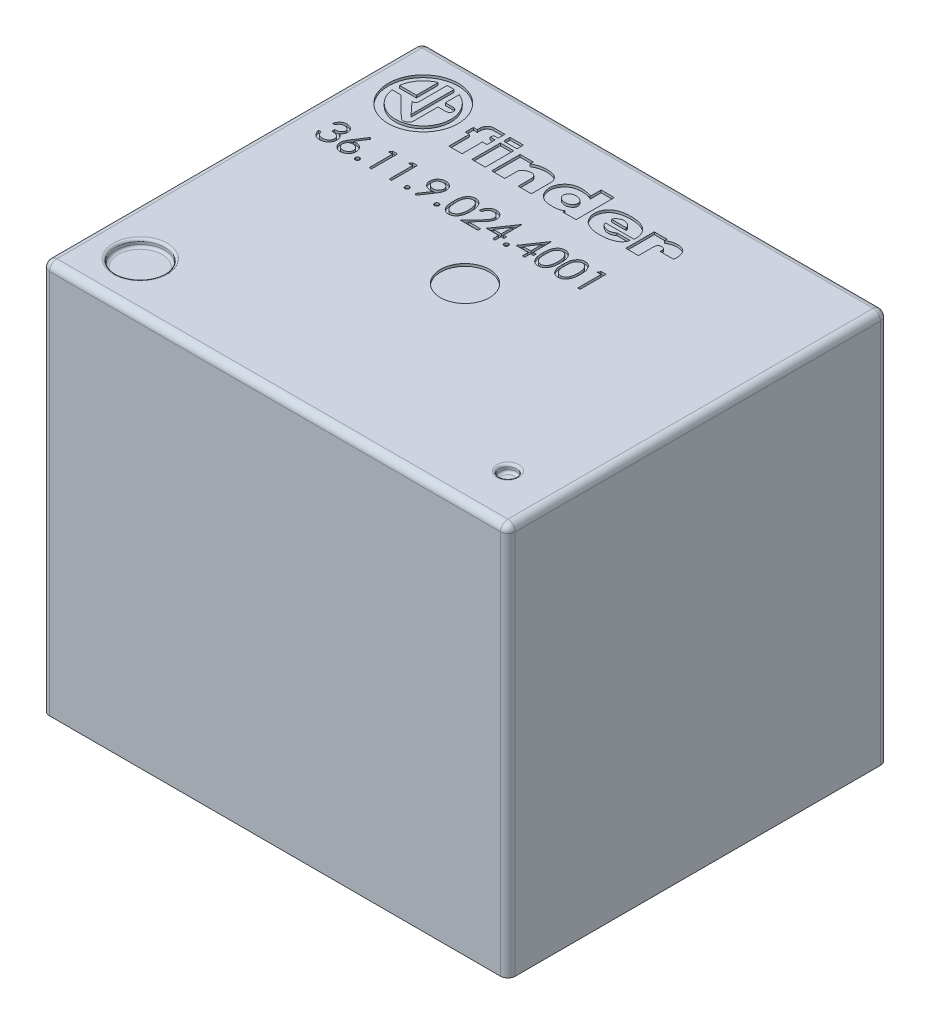
SolidWorks part; units mm, degrees
ref_plane "Front Plane" through (0, 0, 0) normal (0, 0, 1) x (1, 0, 0)
ref_plane "Top Plane" through (0, 0, 0) normal (0, 1, 0) x (1, 0, 0)
ref_plane "Right Plane" through (0, 0, 0) normal (1, 0, 0) x (0, 0, -1)
sketch "Sketch1" plane through (0, 0, 0) normal (0, 1, 0) x (1, 0, 0)
  line L0 (9.5, -7.75) -> (-9.5, 7.75) construction
  line L1 (-9.5, -7.75) -> (9.5, -7.75)
  line L2 (-9.5, -7.75) -> (-9.5, 7.75)
  line L3 (-9.5, 7.75) -> (9.5, 7.75)
  line L4 (9.5, -7.75) -> (9.5, 7.75)
  dimension "D1" = 19
  dimension "D2" = 15.5
extrude "Boss-Extrude1" add sketch "Sketch1" along normal blind 16
sketch "Sketch3" plane through (0, 0, 0) normal (0, -1, 0) x (1, 0, 0)
  line L0 (6.55, 5.75) -> (5.65, 6.25) construction
  line L1 (-6.35, 6.45) -> (-5.85, 6.45)
  line L2 (-6.35, 6.45) -> (-6.35, 5.55)
  line L3 (-6.35, 5.55) -> (-5.85, 5.55)
  line L4 (-5.85, 6.45) -> (-5.85, 5.55)
  line L5 (-8.35, 0.45) -> (-7.85, 0.45)
  line L6 (-8.35, 0.45) -> (-8.35, -0.45)
  line L7 (-8.35, -0.45) -> (-7.85, -0.45)
  line L8 (-7.85, 0.45) -> (-7.85, -0.45)
  line L9 (-6.35, -5.55) -> (-5.85, -5.55)
  line L10 (-6.35, -5.55) -> (-6.35, -6.45)
  line L11 (-6.35, -6.45) -> (-5.85, -6.45)
  line L12 (-5.85, -5.55) -> (-5.85, -6.45)
  line L13 (5.65, -6.25) -> (6.55, -6.25)
  line L14 (5.65, -6.25) -> (5.65, -5.75)
  line L15 (5.65, -5.75) -> (6.55, -5.75)
  line L16 (6.55, -6.25) -> (6.55, -5.75)
  line L17 (5.65, 6.25) -> (6.55, 6.25)
  line L18 (5.65, 6.25) -> (5.65, 5.75)
  line L19 (5.65, 5.75) -> (6.55, 5.75)
  line L20 (6.55, 6.25) -> (6.55, 5.75)
  line L21 (6.55, -5.75) -> (5.65, -6.25) construction
  line L22 (-5.85, 5.55) -> (-6.35, 6.45) construction
  line L23 (-7.85, -0.45) -> (-8.35, 0.45) construction
  line L24 (-5.85, -6.45) -> (-6.35, -5.55) construction
  line L25 (6.1, 6) -> (6.1, -6) construction
  line L26 (-6.1, 6) -> (-4.4393, 6) construction
  line L27 (-6.1, -6) -> (-4.066, -6) construction
  line L28 (-8.1, 0) -> (0, 0) construction
  line L29 (-6.1, 6) -> (-6.1, -6) construction
  line L30 (9.5, 7.75) -> (9.5, -7.75) construction
  dimension "D1" = 6
  dimension "D2" = 6
  dimension "D3" = 2
  dimension "D4" = 12.2
  dimension "D6" = 0.5
  dimension "D7" = 0.9
  dimension "D8" = 3.4
extrude "Boss-Extrude2" add sketch "Sketch3" along normal blind 1
fillet "Fillet1" radius 0.3 8 edges at (0, 16, -7.75) (9.5, 16, 0) (0, 16, 7.75) (-9.5, 16, 0) (-9.5, 8, -7.75) (-9.5, 8, 7.75) (9.5, 8, -7.75) (9.5, 8, 7.75)
sketch "Sketch4" plane through (0, 16, 0) normal (0, 1, 0) x (1, 0, 0)
  line L0 (7.5, -5.75) -> (-7.5, -5.75) construction
  line L1 (9.2, -7.75) -> (-9.2, -7.75) construction
  line L2 (-9.5, -7.45) -> (-9.5, 7.45) construction
  line L3 (9.5, 7.45) -> (9.5, -7.45) construction
  circle A0 centre (-7.5, -5.75) radius 1
  circle A1 centre (7.5, -5.75) radius 0.35
  dimension "D1" = 2
  dimension "D2" = 0.7
  dimension "D3" = 2
  dimension "D4" = 2
  dimension "D5" = 2
extrude "Cut-Extrude1" cut sketch "Sketch4" against normal blind 0.3
fillet "Fillet2" radius 0.1 4 edges at (7.5, 15.7, 6.1) (-7.5, 15.7, 6.75) (7.5, 16, 6.1) (-7.5, 16, 6.75)
sketch "Sketch5" plane through (0, 16, 0) normal (0, 1, 0) x (1, 0, 0)
  circle A0 centre (0, 0) radius 1
  dimension "D1" = 2
extrude "Cut-Extrude2" cut sketch "Sketch5" against normal blind 0.1
sketch "Sketch6" plane through (0, 16, 0) normal (0, 1, 0) x (1, 0, 0)
  line L0 (-7.0766, 6.631) -> (-7.0766, 4.8774)
  line L1 (-7.0766, 4.8774) -> (-7.5192, 5.3576)
  line L2 (-7.5192, 5.3576) -> (-7.4506, 5.3576)
  line L3 (-7.3614, 5.4643) -> (-7.3614, 6.6301)
  line L4 (-7.6461, 6.5542) -> (-7.6461, 5.663)
  line L5 (-7.6461, 5.663) -> (-8.3331, 5.663)
  line L6 (-8.3326, 5.3576) -> (-7.972, 5.3576)
  line L7 (-7.972, 5.3576) -> (-7.1334, 4.5348)
  line L8 (-6.7885, 4.6853) -> (-6.7885, 5.6868)
  line L9 (-6.7885, 5.6868) -> (-6.4489, 5.6868)
  line L10 (-6.4794, 5.9853) -> (-6.7885, 5.9853)
  line L11 (-6.7885, 5.9853) -> (-6.7885, 6.5556)
  line L12 (-2.353, 5.078) -> (-2.353, 4.524)
  line L13 (-2.353, 4.524) -> (-1.8178, 4.524)
  line L14 (-1.8178, 4.524) -> (-1.8178, 5.3317)
  line L15 (-2.8985, 5.5566) -> (-2.8985, 5.6868)
  line L16 (-2.8985, 5.6868) -> (-3.437, 5.6868)
  line L17 (-3.437, 5.6868) -> (-3.437, 4.524)
  line L18 (-3.437, 4.524) -> (-2.8985, 4.524)
  line L19 (-2.8985, 4.524) -> (-2.8985, 5.0644)
  line L20 (0.0105, 6.0815) -> (0.0105, 4.5206)
  line L21 (0.0105, 4.5206) -> (-0.5281, 4.5206)
  line L22 (-0.5281, 5.6303) -> (-0.5281, 6.0815)
  line L23 (-0.5281, 6.0815) -> (0.0105, 6.0815)
  line L24 (2.0344, 5.6868) -> (2.5524, 5.6868)
  line L25 (2.5524, 5.6868) -> (2.5524, 5.584)
  line L26 (3.3996, 5.1107) -> (2.8509, 5.1107)
  line L27 (2.8509, 5.1107) -> (2.8509, 5.1826)
  line L28 (2.5524, 5.169) -> (2.5524, 4.524)
  line L29 (2.5524, 4.524) -> (2.0344, 4.524)
  line L30 (2.0344, 4.524) -> (2.0344, 5.6868)
  line L31 (0.9607, 5.0077) -> (0.9298, 5.0077)
  line L32 (0.9298, 5.0077) -> (0.7239, 5.0077)
  line L33 (1.3174, 4.891) -> (1.8456, 4.891)
  line L34 (1.8766, 5.0112) -> (0.9607, 5.0077)
  line L35 (0.9607, 5.2581) -> (1.3174, 5.2581)
  line L36 (0.7239, 5.2581) -> (0.9607, 5.2581)
  line L37 (-4.4593, 5.8139) -> (-4.4593, 6.0856)
  line L38 (-4.4593, 6.0856) -> (-4.9114, 6.0856)
  line L39 (-5.1831, 5.8139) -> (-5.1831, 5.6868)
  line L40 (-5.1831, 5.6868) -> (-5.3443, 5.6868)
  line L41 (-5.3443, 5.6868) -> (-5.3443, 5.3576)
  line L42 (-5.3443, 5.3576) -> (-5.1831, 5.3576)
  line L43 (-5.1831, 5.3576) -> (-5.1831, 4.524)
  line L44 (-5.1831, 4.524) -> (-4.6445, 4.524)
  line L45 (-4.6445, 4.524) -> (-4.6445, 5.3576)
  line L46 (-4.6445, 5.3576) -> (-4.4593, 5.3576)
  line L47 (-4.4593, 5.3576) -> (-4.4593, 5.6868)
  line L48 (-4.4593, 5.6868) -> (-4.6616, 5.6868)
  line L49 (-4.6616, 5.6868) -> (-4.6472, 5.7649)
  line L50 (-4.5818, 5.8139) -> (-4.4593, 5.8139)
  line L51 (-4.2431, 4.524) -> (-4.2431, 5.6868)
  line L52 (-4.2431, 5.6868) -> (-3.6977, 5.6868)
  line L53 (-3.6977, 5.6868) -> (-3.6977, 4.524)
  line L54 (-3.6977, 4.524) -> (-4.2431, 4.524)
  line L55 (-4.2431, 5.8173) -> (-4.2431, 6.0848)
  line L56 (-4.2431, 6.0848) -> (-3.6977, 6.0848)
  line L57 (-3.6977, 6.0848) -> (-3.6977, 5.8173)
  line L58 (-3.6977, 5.8173) -> (-4.2431, 5.8173)
  line L59 (-0.5281, 5.1174) -> (-0.5281, 5.1621)
  line L60 (-0.5281, 4.5206) -> (-0.5281, 4.6124)
  arc A0 (-4.9114, 6.0856) -> (-5.1831, 5.8139) centre (-4.9114, 5.8139) ccw
  arc A1 (-4.5818, 5.8139) -> (-4.6472, 5.7649) centre (-4.5737, 5.7349) ccw
  arc A2 (-1.8178, 5.3317) -> (-2.0375, 5.6492) centre (-2.183, 5.3138) ccw
  arc A3 (-2.0375, 5.6492) -> (-2.8985, 5.5566) centre (-2.3653, 4.6479) ccw
  arc A4 (-2.353, 5.078) -> (-2.5726, 5.2719) centre (-2.5483, 5.078) ccw
  arc A5 (-2.5726, 5.2719) -> (-2.8985, 5.0644) centre (-2.5524, 4.8804) ccw
  circle A6 centre (-7.2156, 5.512) radius 1.427
  arc A7 (-7.6461, 6.5542) -> (-8.3331, 5.663) centre (-7.2156, 5.512) ccw
  arc A8 (-8.3326, 5.3576) -> (-6.7885, 6.5556) centre (-7.2156, 5.512) ccw
  arc A9 (-7.4506, 5.3576) -> (-7.3614, 5.4643) centre (-7.5002, 5.4898) ccw
  arc A10 (-6.4489, 5.6868) -> (-6.4794, 5.9853) centre (-6.4639, 5.8361) ccw
  arc A11 (-7.0766, 6.631) -> (-7.3614, 6.6301) centre (-7.2156, 5.512) ccw
  spline S0 degree 3 poles (-0.5281, 5.6303) (-0.5414, 5.6421) (-0.5699, 5.6639) (-0.6194, 5.685) (-0.6716, 5.6978) (-0.742, 5.7107) (-0.83, 5.7257) (-0.9368, 5.7321) (-1.0435, 5.7282) (-1.1502, 5.7181) (-1.2536, 5.689) (-1.3513, 5.6443) (-1.4382, 5.581) (-1.5137, 5.5049) (-1.5772, 5.4184) (-1.6239, 5.3216) (-1.6527, 5.2182) (-1.664, 5.1112) (-1.6525, 5.0044) (-1.6256, 4.9006) (-1.581, 4.8028) (-1.5188, 4.7151) (-1.4398, 4.6421) (-1.3502, 4.5833) (-1.2527, 4.5383) (-1.1481, 4.5134) (-1.0414, 4.5051) (-0.9345, 4.505) (-0.8276, 4.5086) (-0.6863, 4.5257) (-0.5855, 4.5709) (-0.5281, 4.6124) knots 0 0 0 0 0.178077 0.355042 0.534345 0.714657 1.07097 1.425797 1.782602 2.138605 2.494666 2.851055 3.206894 3.563377 3.919395 4.27549 4.631811 4.98797 5.344082 5.7004 6.056404 6.412687 6.768555 7.124995 7.48092 7.837066 8.193227 8.549154 8.905929 9.261829 9.97056 9.97056 9.97056 9.97056
  spline S1 degree 3 poles (-0.5281, 5.1621) (-0.5306, 5.1813) (-0.5414, 5.2191) (-0.5739, 5.2682) (-0.6191, 5.3056) (-0.6713, 5.3314) (-0.7267, 5.3488) (-0.7826, 5.3637) (-0.8405, 5.3704) (-0.8985, 5.3639) (-0.9543, 5.3471) (-1.0235, 5.3121) (-1.0942, 5.243) (-1.1258, 5.1456) (-1.1088, 5.0689) (-1.0819, 5.0169) (-1.0436, 4.9725) (-0.9951, 4.9398) (-0.9412, 4.9177) (-0.8851, 4.9027) (-0.8272, 4.8962) (-0.7501, 4.9011) (-0.6752, 4.9261) (-0.6105, 4.9687) (-0.568, 5.0089) (-0.5386, 5.0599) (-0.5298, 5.0982) (-0.5281, 5.1174) knots 0 0 0 0 0.193288 0.38668 0.580072 0.772334 0.965852 1.159369 1.351212 1.544294 1.738459 1.931765 2.315248 2.698535 2.891497 3.08624 3.279347 3.471496 3.665362 3.858867 4.051425 4.244518 4.629048 4.822527 5.015999 5.208857 5.402321 5.402321 5.402321 5.402321
  spline S2 degree 3 poles (1.8766, 5.0112) (1.8841, 5.0383) (1.8935, 5.0945) (1.8869, 5.1797) (1.868, 5.2628) (1.832, 5.37) (1.7614, 5.4945) (1.6548, 5.5897) (1.5588, 5.6489) (1.4812, 5.6833) (1.4004, 5.7089) (1.2908, 5.7357) (1.1506, 5.7548) (0.9813, 5.7573) (0.8122, 5.7467) (0.6458, 5.7145) (0.4846, 5.6603) (0.3419, 5.5647) (0.2371, 5.4292) (0.1713, 5.2717) (0.1533, 5.13) (0.1642, 5.0174) (0.1949, 4.9087) (0.243, 4.8052) (0.312, 4.7157) (0.3697, 4.6535) (0.439, 4.6038) (0.5402, 4.5537) (0.673, 4.5042) (0.8402, 4.4749) (1.009, 4.4624) (1.1784, 4.4703) (1.3184, 4.4897) (1.4284, 4.5154) (1.5085, 4.5431) (1.5854, 4.5783) (1.6608, 4.6171) (1.7279, 4.6697) (1.7821, 4.7351) (1.8256, 4.8082) (1.8411, 4.8632) (1.8456, 4.891) knots 0 0 0 0 0.281176 0.56409 0.848997 1.131205 1.693847 2.256883 2.539007 2.820697 3.102988 3.385255 3.948537 4.512595 5.076291 5.639939 6.203885 6.766738 7.329351 7.892323 8.455148 8.737355 9.018967 9.581781 9.864039 10.146609 10.427657 10.710445 11.274397 11.837822 12.40155 12.964881 13.530137 13.812304 14.093729 14.375757 14.65757 14.939436 15.221201 15.502997 15.784839 15.784839 15.784839 15.784839
  spline S3 degree 3 poles (0.7239, 5.0077) (0.7303, 4.9745) (0.7582, 4.9095) (0.8408, 4.8463) (0.9355, 4.8089) (1.0361, 4.792) (1.1213, 4.7965) (1.1869, 4.814) (1.2485, 4.842) (1.2912, 4.8698) (1.3174, 4.891) knots 0 0 0 0 0.337153 0.674314 1.011743 1.348775 1.687276 1.856094 2.024673 2.361715 2.361715 2.361715 2.361715
  spline S4 degree 3 poles (1.3174, 5.2581) (1.316, 5.2767) (1.3078, 5.3139) (1.278, 5.3626) (1.2367, 5.4013) (1.1886, 5.431) (1.1361, 5.4517) (1.081, 5.464) (1.0244, 5.468) (0.9682, 5.4647) (0.9123, 5.4526) (0.8657, 5.4205) (0.8144, 5.3975) (0.7721, 5.3592) (0.7408, 5.312) (0.728, 5.2763) (0.7239, 5.2581) knots 0 0 0 0 0.186856 0.373575 0.561385 0.74845 0.935589 1.123113 1.311429 1.500242 1.686444 1.873057 2.05952 2.246468 2.434628 2.621194 2.621194 2.621194 2.621194
  spline S5 degree 3 poles (2.8509, 5.1826) (2.8521, 5.2042) (2.8424, 5.249) (2.7968, 5.2991) (2.733, 5.3221) (2.6665, 5.3164) (2.6051, 5.2881) (2.5647, 5.234) (2.5534, 5.1907) (2.5524, 5.169) knots 0 0 0 0 0.216215 0.433393 0.64995 0.869744 1.087238 1.304829 1.522317 1.522317 1.522317 1.522317
  spline S6 degree 3 poles (3.3996, 5.1107) (3.4038, 5.1414) (3.4088, 5.2034) (3.4048, 5.2966) (3.3912, 5.3888) (3.3673, 5.4793) (3.3227, 5.5621) (3.2575, 5.6306) (3.1738, 5.6744) (3.0837, 5.6988) (2.9914, 5.7135) (2.898, 5.7112) (2.8056, 5.6981) (2.6856, 5.6653) (2.6026, 5.6201) (2.5524, 5.584) knots 0 0 0 0 0.309917 0.620117 0.930884 1.240783 1.550959 1.861842 2.17099 2.482795 2.792567 3.102413 3.413424 3.723772 4.342415 4.342415 4.342415 4.342415
  spline S7 degree 3 poles (-6.7885, 4.6853) (-6.79, 4.6635) (-6.8002, 4.6202) (-6.8347, 4.5633) (-6.8866, 4.5216) (-6.9468, 4.495) (-7.0127, 4.4854) (-7.0769, 4.5017) (-7.1155, 4.5224) (-7.1334, 4.5348) knots 0 0 0 0 0.218062 0.436362 0.653729 0.872956 1.08909 1.305405 1.523282 1.523282 1.523282 1.523282
extrude "Cut-Extrude3" cut sketch "Sketch6" against normal blind 0.1
sketch "Sketch7" plane through (0, 16, 0) normal (0, 1, 0) x (1, 0, 0)
  text T0 "36.11.9.024.4001" font "Century Gothic" height in points 4
extrude "Cut-Extrude4" cut sketch "Sketch7" against normal blind 0.1
